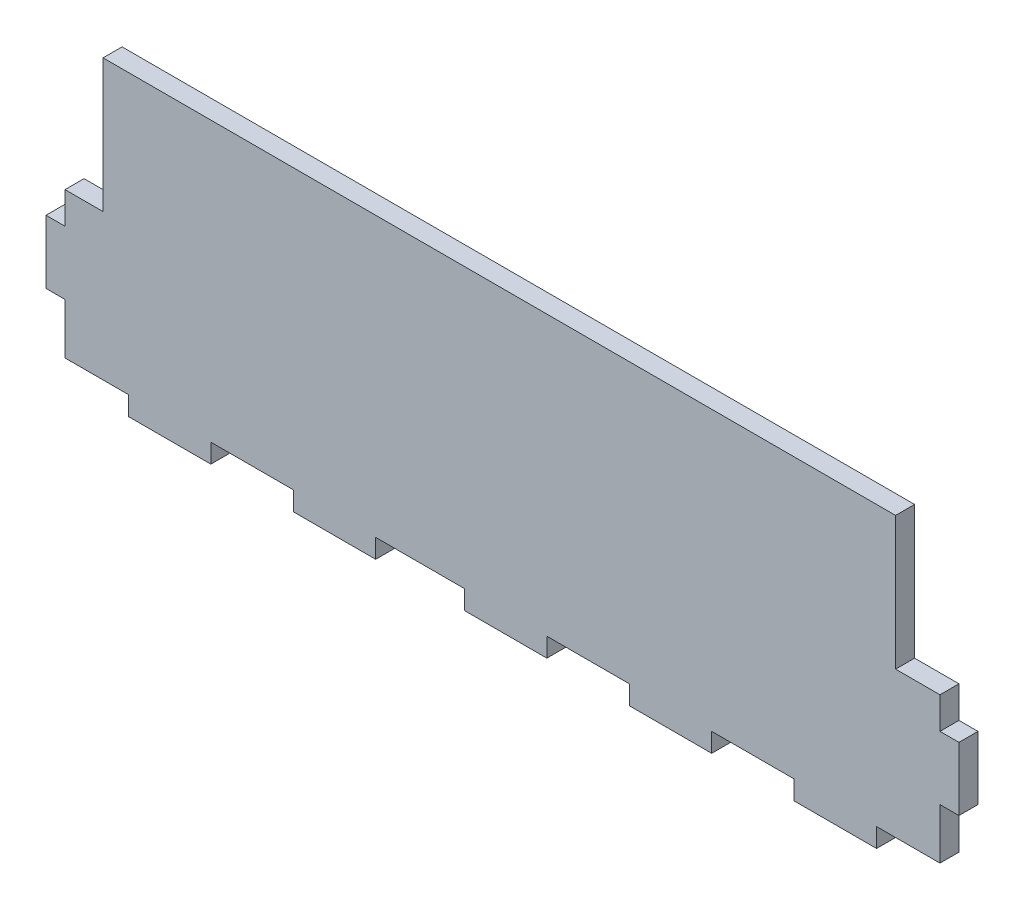
SolidWorks part; units mm, degrees
ref_plane "Front Plane" through (0, 0, 0) normal (0, 0, 1) x (1, 0, 0)
ref_plane "Top Plane" through (0, 0, 0) normal (0, 1, 0) x (1, 0, 0)
ref_plane "Right Plane" through (0, 0, 0) normal (1, 0, 0) x (0, 0, -1)
sketch "Sketch1" plane through (0, 0, 0) normal (0, 0, 1) x (1, 0, 0)
  line L0 (14.6331, 0) -> (27.6331, 0)
  line L1 (0, 0) -> (1.6331, 0)
  line L2 (-2.3669, 23) -> (-2.3669, 44)
  line L3 (-2.3669, 44) -> (122.6331, 44)
  line L4 (122.6331, 23) -> (122.6331, 44)
  line L5 (-2.3669, 23) -> (-8.3669, 23)
  line L6 (40.6331, 0) -> (54.6331, 0)
  line L7 (0, 0) -> (-8.3669, 0)
  line L8 (-8.3669, 23) -> (-8.3669, 18)
  line L9 (125, 0) -> (129.6331, 0)
  line L10 (-8.3669, 8) -> (-8.3669, 0)
  line L11 (122.6331, 23) -> (129.6331, 23)
  line L12 (129.6331, 0) -> (129.6331, 8)
  line L13 (-8.3669, 18) -> (-11.3669, 18)
  line L14 (129.6331, 18) -> (129.6331, 23)
  line L15 (-8.3669, 8) -> (-11.3669, 8)
  line L16 (-11.3669, 18) -> (-11.3669, 8)
  line L17 (129.6331, 18) -> (132.6331, 18)
  line L19 (129.6331, 8) -> (132.6331, 8)
  line L20 (132.6331, 18) -> (132.6331, 8)
  line L21 (67.6331, 0) -> (80.6331, 0)
  line L22 (1.6331, 0) -> (1.6331, -3)
  line L23 (1.6331, -3) -> (14.6331, -3)
  line L24 (14.6331, 0) -> (14.6331, -3)
  line L25 (93.6331, 0) -> (106.6331, 0)
  line L26 (27.6331, 0) -> (27.6331, -3)
  line L27 (27.6331, -3) -> (40.6331, -3)
  line L28 (40.6331, 0) -> (40.6331, -3)
  line L29 (119.6331, 0) -> (125, 0)
  line L30 (54.6331, 0) -> (54.6331, -3)
  line L31 (54.6331, -3) -> (67.6331, -3)
  line L32 (67.6331, 0) -> (67.6331, -3)
  line L34 (80.6331, 0) -> (80.6331, -3)
  line L35 (80.6331, -3) -> (93.6331, -3)
  line L36 (93.6331, 0) -> (93.6331, -3)
  line L38 (106.6331, 0) -> (106.6331, -3)
  line L39 (106.6331, -3) -> (119.6331, -3)
  line L40 (119.6331, 0) -> (119.6331, -3)
  dimension "D1" = 125
  dimension "D2" = 21
  dimension "D3" = 5
  dimension "D4" = 10
  dimension "D5" = 8
  dimension "D6" = 10
  dimension "D7" = 10
  dimension "D8" = 21
  dimension "D9" = 5
  dimension "D10" = 10
  dimension "D11" = 13
  dimension "D12" = 13
  dimension "D13" = 13
  dimension "D14" = 13
  dimension "D15" = 13
  dimension "D16" = 13
  dimension "D17" = 14
  dimension "D18" = 13
  dimension "D19" = 13
  dimension "D20" = 6
  dimension "D21" = 3
  dimension "D22" = 3
  dimension "D23" = 3
extrude "Boss-Extrude1" add sketch "Sketch1" along normal blind 3
